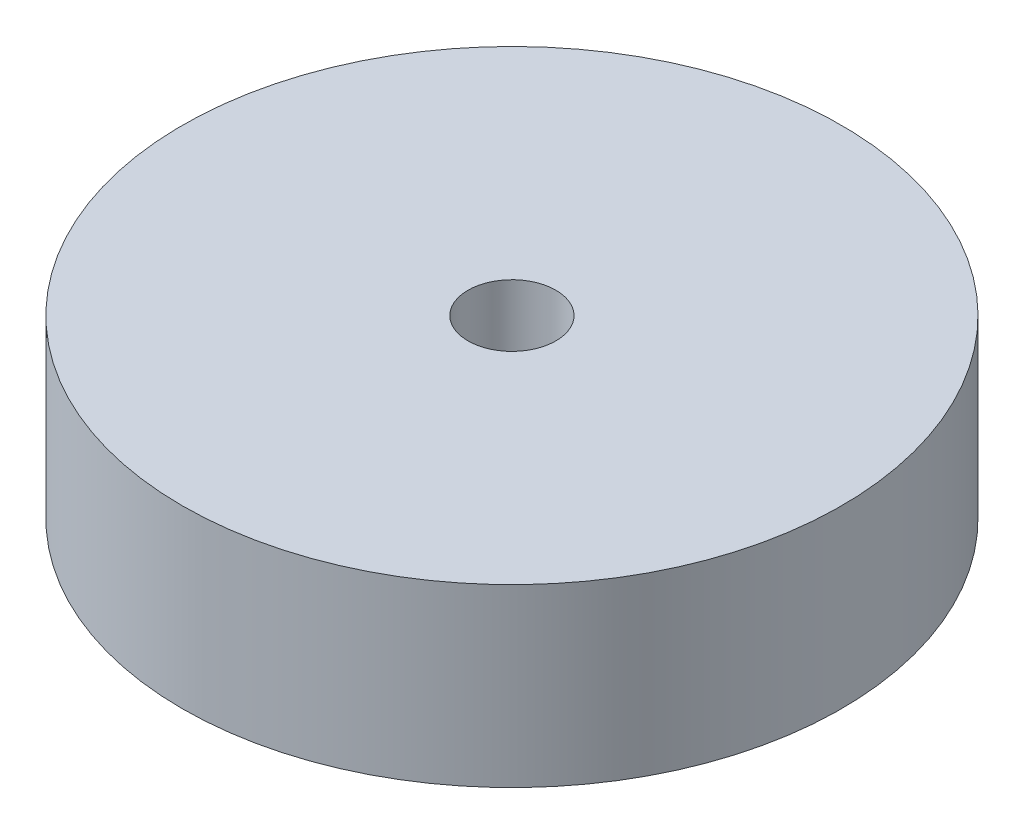
SolidWorks part; units mm, degrees
ref_plane "Front Plane" through (0, 0, 0) normal (0, 0, 1) x (1, 0, 0)
ref_plane "Top Plane" through (0, 0, 0) normal (0, 1, 0) x (1, 0, 0)
ref_plane "Right Plane" through (0, 0, 0) normal (1, 0, 0) x (0, 0, -1)
sketch "Sketch1" plane through (0, 0, 0) normal (0, 1, 0) x (1, 0, 0)
  circle A0 centre (0, 0) radius 47.625
extrude "Boss-Extrude1" add sketch "Sketch1" along normal blind 25.4
sketch "Sketch2" plane through (0, 0, 0) normal (0, -1, 0) x (1, 0, 0)
  circle A0 centre (0, 0) radius 6.35
extrude "Cut-Extrude1" cut sketch "Sketch2" against normal blind 25.4
